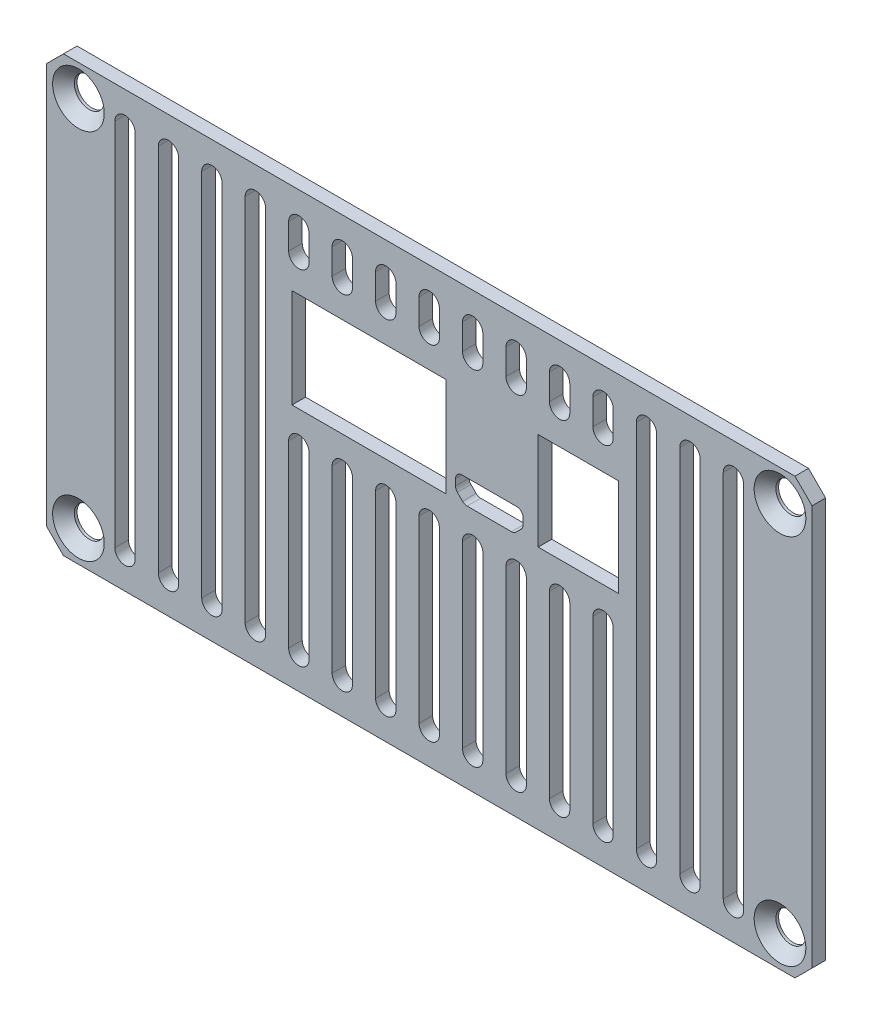
SolidWorks part; units mm, degrees
ref_plane "Front Plane" through (0, 0, 0) normal (0, 0, 1) x (1, 0, 0)
ref_plane "Top Plane" through (0, 0, 0) normal (0, 1, 0) x (1, 0, 0)
ref_plane "Right Plane" through (0, 0, 0) normal (1, 0, 0) x (0, 0, -1)
sketch "Sketch1" plane through (0, 0, 0) normal (0, 0, 1) x (1, 0, 0)
  line L1 (0, 0) -> (89.5, 0)
  line L2 (0, 0) -> (0, 50.8)
  line L3 (0, 50.8) -> (89.5, 50.8)
  line L4 (89.5, 0) -> (89.5, 50.8)
  dimension "D1" = 89.5
  dimension "D2" = 50.8
extrude "Boss-Extrude1" add sketch "Sketch1" along normal blind 1.5875
chamfer "Chamfer1" distance 2 angle 45 4 edges at (0, 0, 0.7937) (89.5, 0, 0.7937) (89.5, 50.8, 0.7937) (0, 50.8, 0.7937)
sketch "Sketch2" plane through (0, 0, 1.5875) normal (0, 0, 1) x (1, 0, 0)
  line L0 (46.4897, 39.9885) -> (28.9129, 39.9885) construction
  line L1 (28.7129, 40.1885) -> (46.6897, 40.1885)
  line L2 (28.7129, 40.1885) -> (28.7129, 28.6125)
  line L3 (28.7129, 28.6125) -> (46.6897, 28.6125)
  line L4 (46.6897, 40.1885) -> (46.6897, 28.6125)
  line L5 (57.4868, 40.0125) -> (66.8868, 40.0125)
  line L6 (57.4868, 40.0125) -> (57.4868, 28.6125)
  line L7 (57.4868, 28.6125) -> (66.8868, 28.6125)
  line L8 (66.8868, 40.0125) -> (66.8868, 28.6125)
  line L9 (28.9129, 39.9885) -> (28.9129, 28.8125) construction
  line L10 (46.4897, 28.8125) -> (46.4897, 39.9885) construction
  line L11 (28.9129, 28.8125) -> (46.4897, 28.8125) construction
  line L12 (66.6868, 39.8125) -> (57.6868, 39.8125) construction
  line L13 (66.6868, 39.8125) -> (66.6868, 28.8125) construction
  line L14 (57.6868, 28.8125) -> (57.6868, 39.8125) construction
  line L15 (57.6868, 28.8125) -> (66.6868, 28.8125) construction
  line L17 (51.7729, 31.4625) -> (51.7729, 28.6125) construction
  line L18 (55.7229, 29.9661) -> (55.7229, 30.7125)
  line L19 (54.8997, 28.8322) -> (55.5033, 29.4357)
  line L62 (54.3694, 28.6125) -> (49.1765, 28.6125)
  line L67 (48.5729, 31.4625) -> (54.9729, 31.4625)
  line L70 (48.6462, 28.8322) -> (48.0426, 29.4357)
  line L73 (47.8229, 29.9661) -> (47.8229, 30.7125)
  arc A0 (54.9729, 31.4625) -> (55.7229, 30.7125) centre (54.9729, 30.7125) cw
  arc A1 (55.7229, 29.9661) -> (55.5033, 29.4357) centre (54.9729, 29.9661) cw
  arc A2 (54.8997, 28.8322) -> (54.3694, 28.6125) centre (54.3694, 29.3625) cw
  arc A3 (55.5229, 30.7125) -> (54.9729, 31.2625) centre (54.9729, 30.7125) ccw construction
  arc A27 (48.6462, 28.8322) -> (49.1765, 28.6125) centre (49.1765, 29.3625) ccw
  arc A28 (47.8229, 29.9661) -> (48.0426, 29.4357) centre (48.5729, 29.9661) ccw
  arc A29 (48.5729, 31.4625) -> (47.8229, 30.7125) centre (48.5729, 30.7125) ccw
  dimension "D11" = 0.75
  dimension "D12" = 135
  dimension "D1" = 0.2
  dimension "D2" = 0.2
  dimension "D3" = 0.2
  dimension "D4" = 0.2
  dimension "D5" = 0.2
  dimension "D6" = 0.2
  dimension "D7" = 0.2
  dimension "D8" = 0.2
  dimension "D9" = 2.85
  dimension "D10" = 3.95
  dimension "D13" = 2.5964
extrude "Cut-Extrude1" cut sketch "Sketch2" against normal through all
sketch "Sketch3" plane through (0, 0, 1.5875) normal (0, 0, 1) x (1, 0, 0)
  line L0 (0, 25.4) -> (89.5, 25.4) construction
  line L1 (0, 48.8) -> (0, 2) construction
  line L2 (89.5, 2) -> (89.5, 48.8) construction
  line L3 (3.75, 47.15) -> (85.75, 47.15) construction
  line L4 (87.5, 50.8) -> (2, 50.8) construction
  line L5 (44.75, 50.8) -> (44.75, 0) construction
  line L6 (2, 0) -> (87.5, 0) construction
  line L7 (85.75, 47.15) -> (85.75, 3.65) construction
  circle A0 centre (3.75, 47.15) radius 1.75
  circle A1 centre (3.75, 3.65) radius 1.75
  circle A2 centre (85.75, 3.65) radius 1.75
  circle A3 centre (85.75, 47.15) radius 1.75
  point P20 (44.75, 47.15)
  point P21 (85.75, 25.4)
  dimension "D1" = 3.5
  dimension "D2" = 82
  dimension "D3" = 43.5
extrude "Cut-Extrude2" cut sketch "Sketch3" against normal through all
chamfer "Chamfer2" distance 1.27 angle 45 4 edges at (5.5, 3.65, 1.5875) (87.5, 3.65, 1.5875) (87.5, 47.15, 1.5875) (5.5, 47.15, 1.5875)
sketch "Sketch4" plane through (0, 0, 1.5875) normal (0, 0, 1) x (1, 0, 0)
  line L0 (44.75, 50.8) -> (44.75, 40.1885) construction
  line L1 (70.15, 46.99) -> (70.15, 3.81) construction
  line L2 (71.3406, 46.99) -> (71.3406, 3.81)
  line L3 (44.75, 46.99) -> (44.75, 43.9985) construction
  line L4 (45.9406, 46.99) -> (45.9406, 43.9985)
  line L5 (43.5594, 46.99) -> (43.5594, 43.9985)
  line L6 (44.75, 24.8025) -> (44.75, 3.81) construction
  line L7 (45.9406, 24.8025) -> (45.9406, 3.81)
  line L8 (43.5594, 24.8025) -> (43.5594, 3.81)
  line L9 (87.5, 50.8) -> (2, 50.8) construction
  line L10 (46.6897, 40.1885) -> (28.7129, 40.1885) construction
  line L11 (44.75, 0) -> (44.75, 28.6125) construction
  line L12 (2, 0) -> (87.5, 0) construction
  line L13 (28.7129, 28.6125) -> (46.6897, 28.6125) construction
  line L14 (49.83, 46.99) -> (49.83, 43.9985) construction
  line L15 (51.0206, 46.99) -> (51.0206, 43.9985)
  line L16 (48.6394, 46.99) -> (48.6394, 43.9985)
  line L17 (49.83, 24.8025) -> (49.83, 3.81) construction
  line L18 (51.0206, 24.8025) -> (51.0206, 3.81)
  line L19 (48.6394, 24.8025) -> (48.6394, 3.81)
  line L20 (54.91, 46.99) -> (54.91, 43.9985) construction
  line L21 (56.1006, 46.99) -> (56.1006, 43.9985)
  line L22 (53.7194, 46.99) -> (53.7194, 43.9985)
  line L23 (54.91, 24.8025) -> (54.91, 3.81) construction
  line L24 (56.1006, 24.8025) -> (56.1006, 3.81)
  line L25 (53.7194, 24.8025) -> (53.7194, 3.81)
  line L26 (59.99, 46.99) -> (59.99, 43.9985) construction
  line L27 (61.1806, 46.99) -> (61.1806, 43.9985)
  line L28 (58.7994, 46.99) -> (58.7994, 43.9985)
  line L29 (59.99, 24.8025) -> (59.99, 3.81) construction
  line L30 (61.1806, 24.8025) -> (61.1806, 3.81)
  line L31 (58.7994, 24.8025) -> (58.7994, 3.81)
  line L32 (65.07, 46.99) -> (65.07, 43.9985) construction
  line L33 (66.2606, 46.99) -> (66.2606, 43.9985)
  line L34 (63.8794, 46.99) -> (63.8794, 43.9985)
  line L35 (65.07, 24.8025) -> (65.07, 3.81) construction
  line L36 (66.2606, 24.8025) -> (66.2606, 3.81)
  line L37 (63.8794, 24.8025) -> (63.8794, 3.81)
  line L38 (68.9594, 46.99) -> (68.9594, 3.81)
  line L39 (44.75, 46.99) -> (49.83, 46.99) construction
  line L40 (49.83, 46.99) -> (54.91, 46.99) construction
  line L41 (54.91, 46.99) -> (59.99, 46.99) construction
  line L42 (59.99, 46.99) -> (65.07, 46.99) construction
  line L43 (65.07, 46.99) -> (70.15, 46.99) construction
  line L44 (75.23, 46.99) -> (75.23, 3.81) construction
  line L45 (76.4206, 46.99) -> (76.4206, 3.81)
  line L46 (74.0394, 46.99) -> (74.0394, 3.81)
  line L47 (80.31, 46.99) -> (80.31, 3.81) construction
  line L48 (81.5006, 46.99) -> (81.5006, 3.81)
  line L49 (79.1194, 46.99) -> (79.1194, 3.81)
  line L50 (70.15, 46.99) -> (75.23, 46.99) construction
  line L51 (19.35, 46.99) -> (14.27, 46.99) construction
  line L54 (34.59, 46.99) -> (29.51, 46.99) construction
  line L55 (39.67, 46.99) -> (34.59, 46.99) construction
  line L56 (9.19, 46.99) -> (9.19, 3.81) construction
  line L57 (7.9994, 46.99) -> (7.9994, 3.81)
  line L58 (10.3806, 46.99) -> (10.3806, 3.81)
  line L59 (14.27, 46.99) -> (14.27, 3.81) construction
  line L60 (13.0794, 46.99) -> (13.0794, 3.81)
  line L61 (15.4606, 46.99) -> (15.4606, 3.81)
  line L62 (19.35, 46.99) -> (19.35, 3.81) construction
  line L63 (18.1594, 46.99) -> (18.1594, 3.81)
  line L64 (20.5406, 46.99) -> (20.5406, 3.81)
  line L65 (24.43, 46.99) -> (24.43, 3.81) construction
  line L66 (23.2394, 46.99) -> (23.2394, 3.81)
  line L67 (25.6206, 46.99) -> (25.6206, 3.81)
  line L71 (29.51, 24.8025) -> (29.51, 3.81) construction
  line L72 (28.3194, 24.8025) -> (28.3194, 3.81)
  line L73 (30.7006, 24.8025) -> (30.7006, 3.81)
  line L74 (29.51, 46.99) -> (29.51, 43.9985) construction
  line L75 (28.3194, 46.99) -> (28.3194, 43.9985)
  line L76 (30.7006, 46.99) -> (30.7006, 43.9985)
  line L77 (34.59, 24.8025) -> (34.59, 3.81) construction
  line L78 (33.3994, 24.8025) -> (33.3994, 3.81)
  line L79 (35.7806, 24.8025) -> (35.7806, 3.81)
  line L80 (34.59, 46.99) -> (34.59, 43.9985) construction
  line L81 (33.3994, 46.99) -> (33.3994, 43.9985)
  line L82 (35.7806, 46.99) -> (35.7806, 43.9985)
  line L83 (39.67, 24.8025) -> (39.67, 3.81) construction
  line L84 (38.4794, 24.8025) -> (38.4794, 3.81)
  line L85 (40.8606, 24.8025) -> (40.8606, 3.81)
  line L86 (39.67, 46.99) -> (39.67, 43.9985) construction
  line L87 (38.4794, 46.99) -> (38.4794, 43.9985)
  line L88 (40.8606, 46.99) -> (40.8606, 43.9985)
  arc A0 (45.9406, 46.99) -> (43.5594, 46.99) centre (44.75, 46.99) ccw
  arc A1 (43.5594, 43.9985) -> (45.9406, 43.9985) centre (44.75, 43.9985) ccw
  arc A2 (45.9406, 24.8025) -> (43.5594, 24.8025) centre (44.75, 24.8025) ccw
  arc A3 (43.5594, 3.81) -> (45.9406, 3.81) centre (44.75, 3.81) ccw
  arc A4 (51.0206, 46.99) -> (48.6394, 46.99) centre (49.83, 46.99) ccw
  arc A5 (48.6394, 43.9985) -> (51.0206, 43.9985) centre (49.83, 43.9985) ccw
  arc A6 (51.0206, 24.8025) -> (48.6394, 24.8025) centre (49.83, 24.8025) ccw
  arc A7 (48.6394, 3.81) -> (51.0206, 3.81) centre (49.83, 3.81) ccw
  arc A8 (56.1006, 46.99) -> (53.7194, 46.99) centre (54.91, 46.99) ccw
  arc A9 (53.7194, 43.9985) -> (56.1006, 43.9985) centre (54.91, 43.9985) ccw
  arc A10 (56.1006, 24.8025) -> (53.7194, 24.8025) centre (54.91, 24.8025) ccw
  arc A11 (53.7194, 3.81) -> (56.1006, 3.81) centre (54.91, 3.81) ccw
  arc A12 (61.1806, 46.99) -> (58.7994, 46.99) centre (59.99, 46.99) ccw
  arc A13 (58.7994, 43.9985) -> (61.1806, 43.9985) centre (59.99, 43.9985) ccw
  arc A14 (61.1806, 24.8025) -> (58.7994, 24.8025) centre (59.99, 24.8025) ccw
  arc A15 (58.7994, 3.81) -> (61.1806, 3.81) centre (59.99, 3.81) ccw
  arc A16 (66.2606, 46.99) -> (63.8794, 46.99) centre (65.07, 46.99) ccw
  arc A17 (63.8794, 43.9985) -> (66.2606, 43.9985) centre (65.07, 43.9985) ccw
  arc A18 (66.2606, 24.8025) -> (63.8794, 24.8025) centre (65.07, 24.8025) ccw
  arc A19 (63.8794, 3.81) -> (66.2606, 3.81) centre (65.07, 3.81) ccw
  arc A20 (71.3406, 46.99) -> (68.9594, 46.99) centre (70.15, 46.99) ccw
  arc A21 (68.9594, 3.81) -> (71.3406, 3.81) centre (70.15, 3.81) ccw
  arc A22 (76.4206, 46.99) -> (74.0394, 46.99) centre (75.23, 46.99) ccw
  arc A23 (74.0394, 3.81) -> (76.4206, 3.81) centre (75.23, 3.81) ccw
  arc A24 (81.5006, 46.99) -> (79.1194, 46.99) centre (80.31, 46.99) ccw
  arc A25 (79.1194, 3.81) -> (81.5006, 3.81) centre (80.31, 3.81) ccw
  arc A26 (7.9994, 46.99) -> (10.3806, 46.99) centre (9.19, 46.99) cw
  arc A27 (10.3806, 3.81) -> (7.9994, 3.81) centre (9.19, 3.81) cw
  arc A28 (13.0794, 46.99) -> (15.4606, 46.99) centre (14.27, 46.99) cw
  arc A29 (15.4606, 3.81) -> (13.0794, 3.81) centre (14.27, 3.81) cw
  arc A30 (18.1594, 46.99) -> (20.5406, 46.99) centre (19.35, 46.99) cw
  arc A31 (20.5406, 3.81) -> (18.1594, 3.81) centre (19.35, 3.81) cw
  arc A32 (23.2394, 46.99) -> (25.6206, 46.99) centre (24.43, 46.99) cw
  arc A33 (25.6206, 3.81) -> (23.2394, 3.81) centre (24.43, 3.81) cw
  arc A36 (28.3194, 24.8025) -> (30.7006, 24.8025) centre (29.51, 24.8025) cw
  arc A37 (30.7006, 3.81) -> (28.3194, 3.81) centre (29.51, 3.81) cw
  arc A38 (28.3194, 46.99) -> (30.7006, 46.99) centre (29.51, 46.99) cw
  arc A39 (30.7006, 43.9985) -> (28.3194, 43.9985) centre (29.51, 43.9985) cw
  arc A40 (33.3994, 24.8025) -> (35.7806, 24.8025) centre (34.59, 24.8025) cw
  arc A41 (35.7806, 3.81) -> (33.3994, 3.81) centre (34.59, 3.81) cw
  arc A42 (33.3994, 46.99) -> (35.7806, 46.99) centre (34.59, 46.99) cw
  arc A43 (35.7806, 43.9985) -> (33.3994, 43.9985) centre (34.59, 43.9985) cw
  arc A44 (38.4794, 24.8025) -> (40.8606, 24.8025) centre (39.67, 24.8025) cw
  arc A45 (40.8606, 3.81) -> (38.4794, 3.81) centre (39.67, 3.81) cw
  arc A46 (38.4794, 46.99) -> (40.8606, 46.99) centre (39.67, 46.99) cw
  arc A47 (40.8606, 43.9985) -> (38.4794, 43.9985) centre (39.67, 43.9985) cw
  point P8 (44.75, 45.4942)
  point P15 (44.75, 14.3062)
  point P30 (49.83, 45.4942)
  point P37 (49.83, 14.3062)
  point P44 (54.91, 45.4942)
  point P51 (54.91, 14.3062)
  point P58 (59.99, 45.4942)
  point P65 (59.99, 14.3062)
  point P72 (65.07, 45.4942)
  point P79 (65.07, 14.3062)
  point P84 (70.15, 25.4)
  point P98 (75.23, 25.4)
  point P105 (80.31, 25.4)
  point P119 (9.19, 25.4)
  point P125 (14.27, 25.4)
  point P131 (19.35, 25.4)
  point P138 (24.43, 25.4)
  point P151 (29.51, 14.3062)
  point P157 (29.51, 45.4942)
  point P164 (34.59, 14.3062)
  point P170 (34.59, 45.4942)
  point P177 (39.67, 14.3062)
  point P183 (39.67, 45.4942)
  dimension "D1" = 2.3813
  dimension "D2" = 3.81
  dimension "D3" = 3.81
  dimension "D4" = 5.08
  dimension "D5" = 5.08
  dimension "D7" = 5.08
  dimension "D8" = 5.08
  dimension "D6" = 3
extrude "Cut-Extrude3" cut sketch "Sketch4" against normal through all
